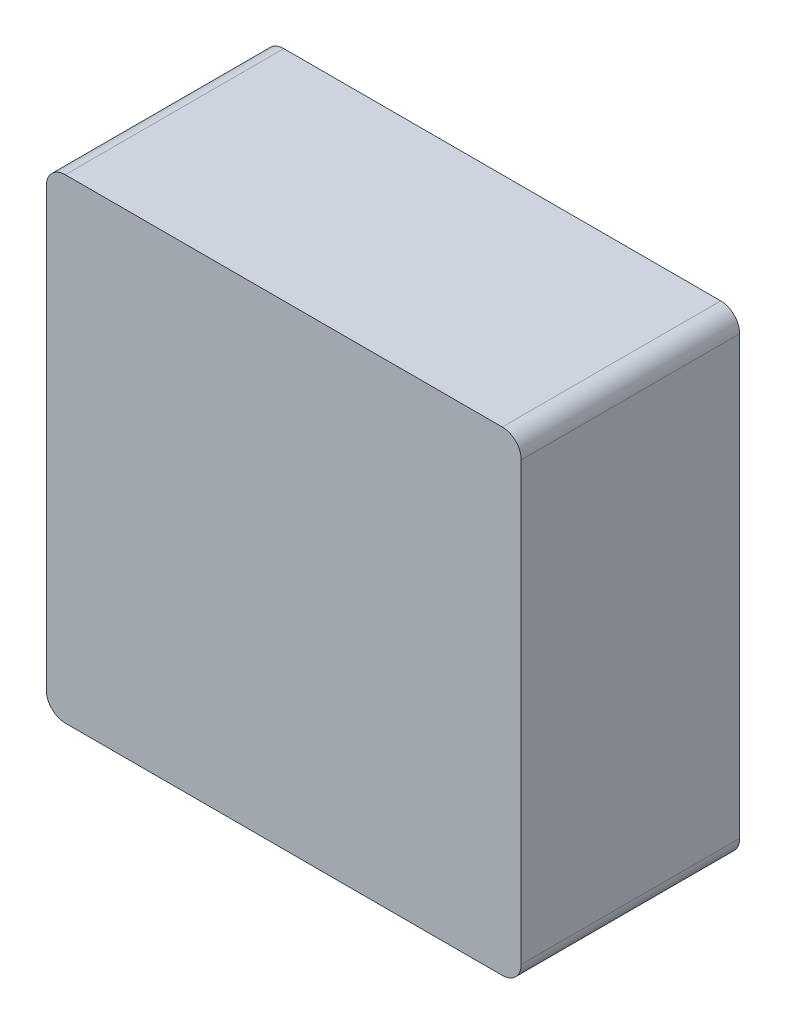
SolidWorks part; units mm, degrees
ref_plane "Płaszczyzna przednia" through (0, 0, 0) normal (0, 0, 1) x (1, 0, 0)
ref_plane "Płaszczyzna górna" through (0, 0, 0) normal (0, 1, 0) x (1, 0, 0)
ref_plane "Płaszczyzna prawa" through (0, 0, 0) normal (1, 0, 0) x (0, 0, -1)
sketch "Szkic1" plane through (0, 0, 0) normal (0, 0, 1) x (1, 0, 0)
  line L0 (21, 23) -> (-21, 23) construction
  line L1 (-15, 20) -> (15, 20)
  line L2 (-15, 20) -> (-15, 23)
  line L3 (-15, 23) -> (15, 23)
  line L4 (15, 20) -> (15, 23)
  line L5 (-15, 20) -> (15, 23) construction
  line L6 (-15, 23) -> (15, 20) construction
  line L7 (20, 15) -> (23, 15)
  line L8 (20, 15) -> (20, -15)
  line L9 (20, -15) -> (23, -15)
  line L10 (23, 15) -> (23, -15)
  line L11 (15, -20) -> (15, -23)
  line L12 (15, -20) -> (-15, -20)
  line L13 (-15, -20) -> (-15, -23)
  line L14 (15, -23) -> (-15, -23)
  line L15 (-20, -15) -> (-23, -15)
  line L16 (-20, -15) -> (-20, 15)
  line L17 (-20, 15) -> (-23, 15)
  line L18 (-23, -15) -> (-23, 15)
  point P0 (0, 21.5)
  dimension "D1" = 3
  dimension "D2" = 30
  dimension "D3" = 4
extrude "Dodanie-wyciągnięcie1" add sketch "Szkic1" against normal blind 2 and the other way blind 23
sketch "Szkic2" plane through (0, 0, 0) normal (0, 0, 1) x (1, 0, 0)
  line L0 (23, 25) -> (-23, 25) construction
  line L1 (-25, -25) -> (25, -25)
  line L2 (-25, -25) -> (-25, 25)
  line L3 (-25, 25) -> (25, 25)
  line L4 (25, -25) -> (25, 25)
  line L5 (-25, -25) -> (25, 25) construction
  line L6 (-25, 25) -> (25, -25) construction
  line L7 (25, -23) -> (25, 23) construction
  line L8 (23, -21) -> (23, 21) construction
  line L9 (-21, -23) -> (21, -23)
  line L10 (-23, -21) -> (-23, 21)
  line L11 (-21, 23) -> (21, 23)
  line L12 (23, -21) -> (23, 21)
  line L13 (-23, -23) -> (23, 23) construction
  line L14 (-23, 23) -> (23, -23) construction
  arc A0 (-21, 23) -> (-23, 21) centre (-21, 21) ccw
  arc A1 (-23, -21) -> (-21, -23) centre (-21, -21) ccw
  arc A2 (23, -21) -> (21, -23) centre (21, -21) cw
  arc A3 (23, 21) -> (21, 23) centre (21, 21) ccw
  point P0 (0, 0)
  point P10 (0, 0)
  dimension "D1" = 2
extrude "Dodanie-wyciągnięcie2" add sketch "Szkic2" along normal up to surface (23 mm away) up to face at (-21.5, 0, 23)
sketch "Szkic3" plane through (0, 0, 23) normal (0, 0, 1) x (1, 0, 0)
  line L0 (23, -21) -> (23, -15) construction
  line L1 (-1.9, 9.9) -> (9.9, 9.9)
  line L2 (-1.9, 9.9) -> (-1.9, -12.6)
  line L3 (-1.9, -12.6) -> (9.9, -12.6)
  line L4 (9.9, 9.9) -> (9.9, -12.6)
  line L5 (-1.9, 9.9) -> (9.9, 9.9)
  line L6 (-1.9, 9.9) -> (-1.9, 14.6)
  line L7 (-1.9, 14.6) -> (9.9, 14.6)
  line L8 (9.9, 9.9) -> (9.9, 14.6)
  line L9 (9.9, -12.6) -> (-1.9, -12.6)
  line L10 (9.9, -12.6) -> (9.9, -17.3)
  line L11 (9.9, -17.3) -> (-1.9, -17.3)
  line L12 (-1.9, -12.6) -> (-1.9, -17.3)
  line L13 (23, -17.3) -> (-23, -17.3)
  line L14 (23, -17.3) -> (23, -12.8)
  line L15 (23, -12.8) -> (-23, -12.8)
  line L16 (-23, -17.3) -> (-23, -12.8)
  line L17 (-23, -15) -> (-23, -21) construction
  line L18 (-20, -15) -> (-20, 15) construction
  line L19 (-20, 10.1) -> (20, 10.1)
  line L20 (-20, 10.1) -> (-20, 14.6)
  line L21 (-20, 14.6) -> (20, 14.6)
  line L22 (20, 10.1) -> (20, 14.6)
  line L23 (20, 15) -> (20, -15) construction
  circle A0 centre (4, 4) radius 8.25 construction
  circle A1 centre (4, -15) radius 1
  circle A2 centre (4, 12.3) radius 1
  point P32 (4, 14.6)
  point P34 (4, -17.3)
  line M27 (20, 15) -> (20, -15)
  line M28 (20, -15) -> (23, -15)
  line M29 (23, -15) -> (23, -21)
  line M37 (-23, -21) -> (-23, -15)
  line M38 (-23, -15) -> (-20, -15)
  line M39 (-20, -15) -> (-20, 15)
  dimension "D1" = 5.9
  dimension "D4" = 5.9
  dimension "D7" = 2
  dimension "D12" = 2
  dimension "D2" = 11.8
  dimension "D3" = 22.5
  dimension "D5" = 4.7
  dimension "D6" = 4.7
  dimension "D8" = 2.3
  dimension "D9" = 2.3
  dimension "D10" = 0.2
  dimension "D11" = 0.2
extrude "Dodanie-wyciągnięcie3" add sketch "Szkic3" against normal blind 23 contours L12 L15 L13 M39 M38 M37 | L10 L15 L12 L11 A1 | L15 L10 L13 M27 M29 M28 | L21 L8 L19 M27 | L6 L19 L8 L7 A2 | L21 L19 L6 M39
fillet "Zaokrąglenie1" radius 2 4 edges at (-25, -25, 11.5) (-25, 25, 11.5) (25, 25, 11.5) (25, -25, 11.5)
sketch "Szkic4" plane through (-25, 0, 0) normal (-1, 0, 0) x (0, 0, 1)
  line L0 (23, 23) -> (23, -23) construction
  line L1 (23, -12.8) -> (23, 10.1) construction
  circle A0 centre (10, -1.35) radius 6.5
  point P11 (23, -1.35)
  dimension "D1" = 13
  dimension "D2" = 13
extrude "Wytnij-wyciągnięcie1" cut sketch "Szkic4" against normal up to next
sketch "Szkic5" plane through (0, 0, 23) normal (0, 0, 1) x (1, 0, 0)
  line L1 (-23, -23) -> (23, -23)
  line L2 (-23, -23) -> (-23, 23)
  line L3 (-23, 23) -> (23, 23)
  line L4 (23, -23) -> (23, 23)
  line L5 (-23, -23) -> (23, 23) construction
  line L6 (-23, 23) -> (23, -23) construction
  point P0 (0, 0)
extrude "Dodanie-wyciągnięcie4" add sketch "Szkic5" against normal blind 2
sketch "Szkic6" plane through (0, 0, 0) normal (0, 0, -1) x (-1, 0, 0)
  circle A0 centre (-4, 12.25) radius 1.05
  circle A1 centre (-4, 4) radius 8.25 construction
  circle A2 centre (-4, -15) radius 1
extrude "Dodanie-wyciągnięcie5" add sketch "Szkic6" against normal up to surface (11 mm away) from offset 10 up to face at (0, -1.35, 21)
